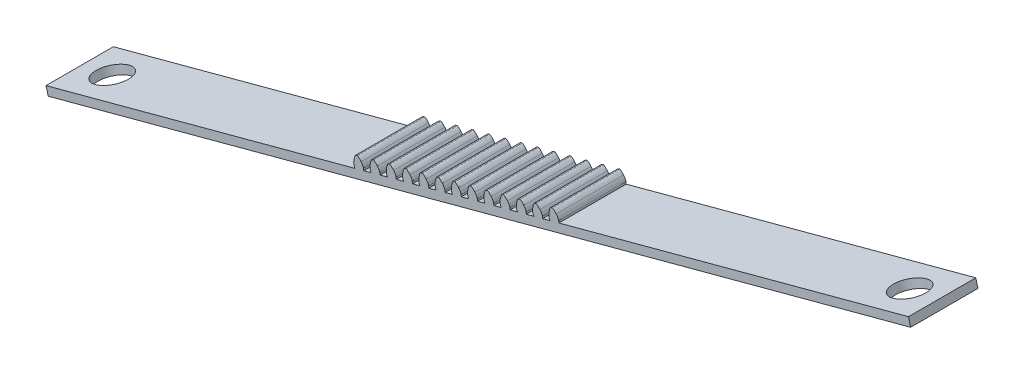
SolidWorks part; units mm, degrees
ref_plane "Front" through (0, 0, 0) normal (0, 0, 1) x (1, 0, 0)
ref_plane "Top" through (0, 0, 0) normal (0, 1, 0) x (1, 0, 0)
ref_plane "Right" through (0, 0, 0) normal (1, 0, 0) x (0, 0, -1)
sketch "Sketch1" plane through (0, 0, 0) normal (0, 0, 1) x (1, 0, 0)
  line L4 (134.3507, -1.879) -> (134.3507, 1.296)
  line L6 (-13.353, 5.1734) -> (-16.689, 4.2795)
  line L9 (-16.689, 4.2795) -> (-15.8673, 1.2127)
  line L10 (-15.8673, 1.2127) -> (202.1663, 59.6346)
  line L12 (201.3446, 62.7014) -> (-13.353, 5.1734)
  line L40 (44.9648, 25.1193) -> (45.506, 25.2643)
  line L41 (44.6473, 20.7145) -> (44.3481, 21.3797)
  line L42 (47.9833, 21.6084) -> (47.9098, 22.3341)
  line L43 (51.0984, 26.7628) -> (51.6396, 26.9078)
  line L44 (50.7809, 22.358) -> (50.4817, 23.0232)
  line L45 (54.117, 23.2519) -> (54.0435, 23.9776)
  line L46 (57.232, 28.4063) -> (57.7732, 28.5513)
  line L47 (56.9145, 24.0015) -> (56.6153, 24.6667)
  line L48 (60.2506, 24.8954) -> (60.1771, 25.6211)
  line L49 (63.3656, 30.0498) -> (63.9069, 30.1948)
  line L50 (63.0481, 25.645) -> (62.749, 26.3102)
  line L51 (66.3842, 26.5389) -> (66.3107, 27.2646)
  line L52 (69.4993, 31.6933) -> (70.0405, 31.8383)
  line L53 (69.1818, 27.2885) -> (68.8826, 27.9537)
  line L54 (72.5178, 28.1824) -> (72.4444, 28.9081)
  line L55 (75.6329, 33.3368) -> (76.1741, 33.4818)
  line L56 (75.3154, 28.932) -> (75.0162, 29.5972)
  line L57 (78.6515, 29.8259) -> (78.578, 30.5516)
  line L58 (81.7665, 34.9803) -> (82.3078, 35.1253)
  line L59 (81.449, 30.5755) -> (81.1498, 31.2407)
  line L60 (84.7851, 31.4694) -> (84.7116, 32.1951)
  line L61 (87.9002, 36.6238) -> (88.4414, 36.7688)
  line L62 (87.5827, 32.219) -> (87.2835, 32.8842)
  line L63 (90.9187, 33.1129) -> (90.8452, 33.8386)
  line L64 (94.0338, 38.2673) -> (94.575, 38.4123)
  line L65 (93.7163, 33.8625) -> (93.4171, 34.5277)
  line L66 (97.0524, 34.7564) -> (96.9789, 35.4821)
  line L67 (100.1674, 39.9108) -> (100.7087, 40.0558)
  line L68 (99.8499, 35.506) -> (99.5507, 36.1712)
  line L69 (103.186, 36.3999) -> (103.1125, 37.1256)
  line L70 (106.301, 41.5543) -> (106.8423, 41.6993)
  line L71 (105.9836, 37.1495) -> (105.6844, 37.8147)
  line L72 (109.3196, 38.0434) -> (109.2461, 38.7691)
  line L73 (112.4347, 43.1978) -> (112.9759, 43.3428)
  line L74 (112.1172, 38.793) -> (111.818, 39.4582)
  line L75 (115.4533, 39.6869) -> (115.3798, 40.4126)
  line L76 (118.5683, 44.8413) -> (119.1095, 44.9863)
  line L77 (118.2508, 40.4365) -> (117.9516, 41.1017)
  line L78 (121.5869, 41.3304) -> (121.5134, 42.0561)
  line L88 (201.3446, 62.7014) -> (202.1663, 59.6346)
  spline S40 degree 2 poles (44.3481, 21.3797) (44.0855, 22.3412) (44.2843, 23.3263) knots 0 0 0 1 1 1
  spline S41 degree 3 poles (44.2843, 23.3263) (44.3692, 23.8195) (44.536, 24.4774) (44.7859, 25.0639) (44.9648, 25.1193) knots 0 0 0 0 0.774836 1 1 1 1
  spline S42 degree 3 poles (46.9918, 24.0518) (46.6716, 24.4365) (46.1982, 24.9228) (45.6885, 25.3057) (45.506, 25.2643) knots 0 0 0 0 0.774836 1 1 1 1
  spline S43 degree 2 poles (47.9098, 22.3341) (47.6565, 23.298) (46.9918, 24.0518) knots 0 0 0 1 1 1
  spline S44 degree 2 poles (50.4817, 23.0232) (50.2192, 23.9847) (50.4179, 24.9698) knots 0 0 0 1 1 1
  spline S45 degree 3 poles (50.4179, 24.9698) (50.5028, 25.463) (50.6696, 26.1209) (50.9196, 26.7074) (51.0984, 26.7628) knots 0 0 0 0 0.774836 1 1 1 1
  spline S46 degree 3 poles (53.1254, 25.6953) (52.8053, 26.08) (52.3318, 26.5663) (51.8222, 26.9492) (51.6396, 26.9078) knots 0 0 0 0 0.774836 1 1 1 1
  spline S47 degree 2 poles (54.0435, 23.9776) (53.7901, 24.9415) (53.1254, 25.6953) knots 0 0 0 1 1 1
  spline S48 degree 2 poles (56.6153, 24.6667) (56.3528, 25.6282) (56.5515, 26.6133) knots 0 0 0 1 1 1
  spline S49 degree 3 poles (56.5515, 26.6133) (56.6364, 27.1065) (56.8033, 27.7644) (57.0532, 28.3509) (57.232, 28.4063) knots 0 0 0 0 0.774836 1 1 1 1
  spline S50 degree 3 poles (59.259, 27.3388) (58.9389, 27.7235) (58.4655, 28.2098) (57.9558, 28.5927) (57.7732, 28.5513) knots 0 0 0 0 0.774836 1 1 1 1
  spline S51 degree 2 poles (60.1771, 25.6211) (59.9237, 26.585) (59.259, 27.3388) knots 0 0 0 1 1 1
  spline S52 degree 2 poles (62.749, 26.3102) (62.4864, 27.2717) (62.6852, 28.2568) knots 0 0 0 1 1 1
  spline S53 degree 3 poles (62.6852, 28.2568) (62.7701, 28.75) (62.9369, 29.4079) (63.1868, 29.9944) (63.3656, 30.0498) knots 0 0 0 0 0.774836 1 1 1 1
  spline S54 degree 3 poles (65.3927, 28.9823) (65.0725, 29.367) (64.5991, 29.8533) (64.0894, 30.2362) (63.9069, 30.1948) knots 0 0 0 0 0.774836 1 1 1 1
  spline S55 degree 2 poles (66.3107, 27.2646) (66.0573, 28.2285) (65.3927, 28.9823) knots 0 0 0 1 1 1
  spline S56 degree 2 poles (68.8826, 27.9537) (68.62, 28.9152) (68.8188, 29.9003) knots 0 0 0 1 1 1
  spline S57 degree 3 poles (68.8188, 29.9003) (68.9037, 30.3935) (69.0705, 31.0514) (69.3205, 31.6379) (69.4993, 31.6933) knots 0 0 0 0 0.774836 1 1 1 1
  spline S58 degree 3 poles (71.5263, 30.6258) (71.2062, 31.0105) (70.7327, 31.4968) (70.2231, 31.8797) (70.0405, 31.8383) knots 0 0 0 0 0.774836 1 1 1 1
  spline S59 degree 2 poles (72.4444, 28.9081) (72.191, 29.872) (71.5263, 30.6258) knots 0 0 0 1 1 1
  spline S60 degree 2 poles (75.0162, 29.5972) (74.7537, 30.5587) (74.9524, 31.5438) knots 0 0 0 1 1 1
  spline S61 degree 3 poles (74.9524, 31.5438) (75.0373, 32.037) (75.2042, 32.6949) (75.4541, 33.2814) (75.6329, 33.3368) knots 0 0 0 0 0.774836 1 1 1 1
  spline S62 degree 3 poles (77.6599, 32.2693) (77.3398, 32.654) (76.8663, 33.1403) (76.3567, 33.5232) (76.1741, 33.4818) knots 0 0 0 0 0.774836 1 1 1 1
  spline S63 degree 2 poles (78.578, 30.5516) (78.3246, 31.5155) (77.6599, 32.2693) knots 0 0 0 1 1 1
  spline S64 degree 2 poles (81.1498, 31.2407) (80.8873, 32.2022) (81.086, 33.1873) knots 0 0 0 1 1 1
  spline S65 degree 3 poles (81.086, 33.1873) (81.1709, 33.6805) (81.3378, 34.3384) (81.5877, 34.9249) (81.7665, 34.9803) knots 0 0 0 0 0.774836 1 1 1 1
  spline S66 degree 3 poles (83.7935, 33.9128) (83.4734, 34.2975) (83, 34.7838) (82.4903, 35.1667) (82.3078, 35.1253) knots 0 0 0 0 0.774836 1 1 1 1
  spline S67 degree 2 poles (84.7116, 32.1951) (84.4582, 33.159) (83.7935, 33.9128) knots 0 0 0 1 1 1
  spline S68 degree 2 poles (87.2835, 32.8842) (87.0209, 33.8457) (87.2197, 34.8309) knots 0 0 0 1 1 1
  spline S69 degree 3 poles (87.2197, 34.8309) (87.3046, 35.324) (87.4714, 35.9819) (87.7213, 36.5684) (87.9002, 36.6238) knots 0 0 0 0 0.774836 1 1 1 1
  spline S70 degree 3 poles (89.9272, 35.5563) (89.607, 35.941) (89.1336, 36.4273) (88.6239, 36.8102) (88.4414, 36.7688) knots 0 0 0 0 0.774836 1 1 1 1
  spline S71 degree 2 poles (90.8452, 33.8386) (90.5919, 34.8025) (89.9272, 35.5563) knots 0 0 0 1 1 1
  spline S72 degree 2 poles (93.4171, 34.5277) (93.1546, 35.4892) (93.3533, 36.4744) knots 0 0 0 1 1 1
  spline S73 degree 3 poles (93.3533, 36.4744) (93.4382, 36.9675) (93.6051, 37.6254) (93.855, 38.2119) (94.0338, 38.2673) knots 0 0 0 0 0.774836 1 1 1 1
  spline S74 degree 3 poles (96.0608, 37.1998) (95.7407, 37.5845) (95.2672, 38.0708) (94.7576, 38.4537) (94.575, 38.4123) knots 0 0 0 0 0.774836 1 1 1 1
  spline S75 degree 2 poles (96.9789, 35.4821) (96.7255, 36.446) (96.0608, 37.1998) knots 0 0 0 1 1 1
  spline S76 degree 2 poles (99.5507, 36.1712) (99.2882, 37.1327) (99.4869, 38.1179) knots 0 0 0 1 1 1
  spline S77 degree 3 poles (99.4869, 38.1179) (99.5718, 38.611) (99.7387, 39.2689) (99.9886, 39.8554) (100.1674, 39.9108) knots 0 0 0 0 0.774836 1 1 1 1
  spline S78 degree 3 poles (102.1944, 38.8433) (101.8743, 39.228) (101.4009, 39.7143) (100.8912, 40.0972) (100.7087, 40.0558) knots 0 0 0 0 0.774836 1 1 1 1
  spline S79 degree 2 poles (103.1125, 37.1256) (102.8591, 38.0895) (102.1944, 38.8433) knots 0 0 0 1 1 1
  spline S80 degree 2 poles (105.6844, 37.8147) (105.4218, 38.7762) (105.6206, 39.7614) knots 0 0 0 1 1 1
  spline S81 degree 3 poles (105.6206, 39.7614) (105.7055, 40.2546) (105.8723, 40.9124) (106.1222, 41.4989) (106.301, 41.5543) knots 0 0 0 0 0.774836 1 1 1 1
  spline S82 degree 3 poles (108.3281, 40.4868) (108.0079, 40.8715) (107.5345, 41.3578) (107.0248, 41.7407) (106.8423, 41.6993) knots 0 0 0 0 0.774836 1 1 1 1
  spline S83 degree 2 poles (109.2461, 38.7691) (108.9928, 39.733) (108.3281, 40.4868) knots 0 0 0 1 1 1
  spline S84 degree 2 poles (111.818, 39.4582) (111.5554, 40.4197) (111.7542, 41.4049) knots 0 0 0 1 1 1
  spline S85 degree 3 poles (111.7542, 41.4049) (111.8391, 41.8981) (112.0059, 42.5559) (112.2559, 43.1424) (112.4347, 43.1978) knots 0 0 0 0 0.774836 1 1 1 1
  spline S86 degree 3 poles (114.4617, 42.1303) (114.1416, 42.515) (113.6681, 43.0013) (113.1585, 43.3842) (112.9759, 43.3428) knots 0 0 0 0 0.774836 1 1 1 1
  spline S87 degree 2 poles (115.3798, 40.4126) (115.1264, 41.3765) (114.4617, 42.1303) knots 0 0 0 1 1 1
  spline S88 degree 2 poles (117.9516, 41.1017) (117.6891, 42.0632) (117.8878, 43.0484) knots 0 0 0 1 1 1
  spline S89 degree 3 poles (117.8878, 43.0484) (117.9727, 43.5416) (118.1396, 44.1994) (118.3895, 44.7859) (118.5683, 44.8413) knots 0 0 0 0 0.774836 1 1 1 1
  spline S90 degree 3 poles (120.5953, 43.7738) (120.2752, 44.1585) (119.8018, 44.6448) (119.2921, 45.0277) (119.1095, 44.9863) knots 0 0 0 0 0.774836 1 1 1 1
  spline S91 degree 2 poles (121.5134, 42.0561) (121.26, 43.02) (120.5953, 43.7738) knots 0 0 0 1 1 1
  dimension "D3" = 24
  dimension "D4" = 5
  dimension "D5" = 9
extrude "Boss-Extrude1" add sketch "Sketch1" along normal blind 25.4
sketch "Sketch2" plane through (-14.5012, -3.8856, 0) normal (-0.9659, -0.2588, 0) x (0, 0, 1)
  line L1 (0, 8.4531) -> (25.4, 8.4531)
  line L2 (0, 8.4531) -> (0, 5.2781)
  line L3 (0, 5.2781) -> (25.4, 5.2781)
  line L4 (25.4, 8.4531) -> (25.4, 5.2781)
extrude "Boss-Extrude2" add sketch "Sketch2" along normal blind 57.15
sketch "Sketch3" plane through (203.5324, 54.5363, 0) normal (0.9659, 0.2588, 0) x (0, 0, -1)
  line L1 (-25.4, 8.4531) -> (0, 8.4531)
  line L2 (-25.4, 8.4531) -> (-25.4, 5.2781)
  line L3 (-25.4, 5.2781) -> (0, 5.2781)
  line L4 (0, 8.4531) -> (0, 5.2781)
extrude "Boss-Extrude3" add sketch "Sketch3" along normal blind 53.975
sketch "Sketch4" plane through (-2.1878, 8.1651, 0) normal (-0.2588, 0.9659, 0) x (0.9659, 0.2588, 0)
  line L0 (-72.1628, -25.4) -> (48.4872, -25.4) construction
  line L1 (-72.1628, -25.4) -> (-72.1628, 0) construction
  circle A0 centre (-59.4628, -12.7) radius 6.35
  dimension "D3" = 12.7
  dimension "D1" = 12.7
  dimension "D2" = 12.7
extrude "Cut-Extrude3" cut sketch "Sketch4" against normal blind 25.4
sketch "Sketch5" plane through (-2.1878, 8.1651, 0) normal (-0.2588, 0.9659, 0) x (0.9659, 0.2588, 0)
  line L0 (264.6872, 0) -> (264.6872, -25.4) construction
  line L2 (264.6872, 0) -> (128.141, 0) construction
  circle A0 centre (251.9872, -12.7) radius 6.35
  dimension "D3" = 12.7
  dimension "D1" = 12.7
  dimension "D2" = 12.7
extrude "Cut-Extrude4" cut sketch "Sketch5" against normal blind 10
